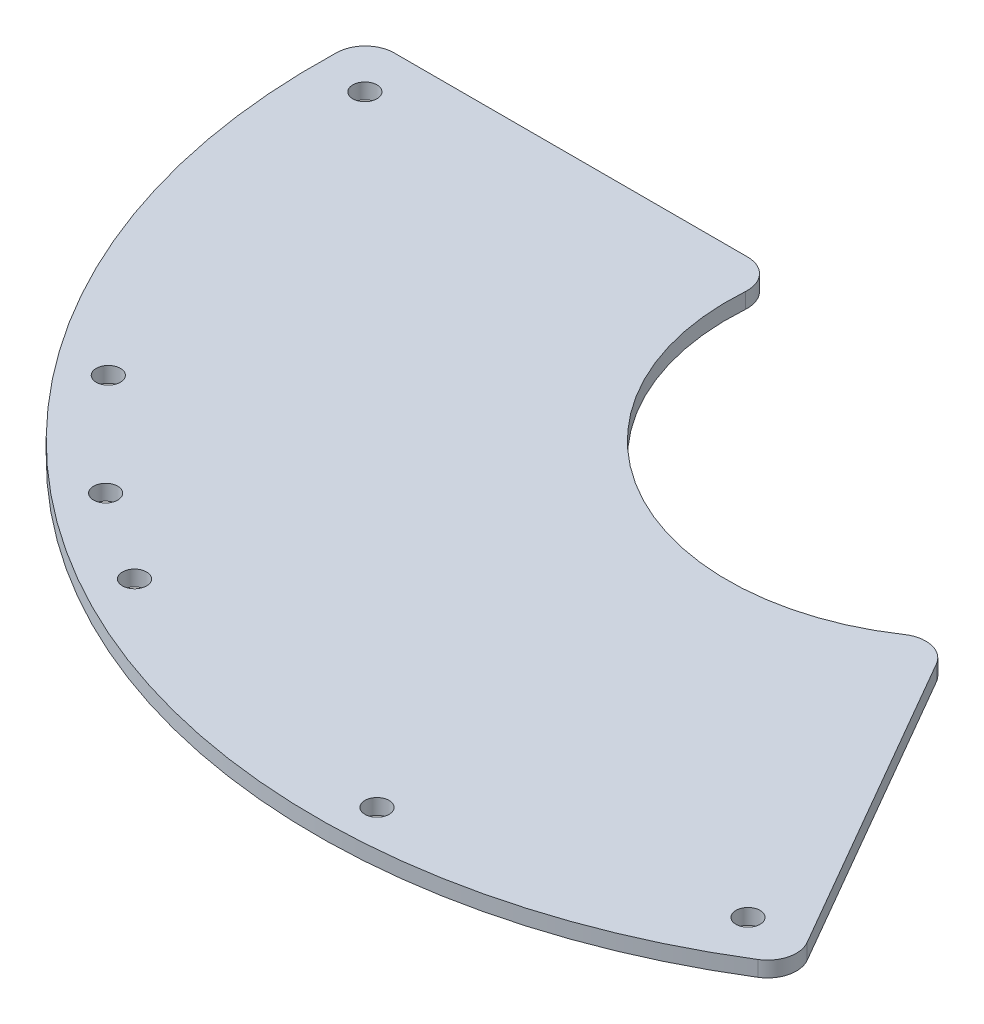
SolidWorks part; units mm, degrees
material "Thornel VCB-20 Carbon Cloth"
ref_plane "Front Plane" through (0, 0, 0) normal (0, 0, 1) x (1, 0, 0)
ref_plane "Top Plane" through (0, 0, 0) normal (0, 1, 0) x (1, 0, 0)
ref_plane "Right Plane" through (0, 0, 0) normal (1, 0, 0) x (0, 0, -1)
sketch "Sketch1" plane through (0, 0, 0) normal (0, 1, 0) x (1, 0, 0)
  line L0 (0, 0) -> (42.3981, -73.4357) construction
  line L1 (0, 0) -> (33.75, -58.4567) construction
  line L2 (0, 0) -> (-67.5, 0) construction
  line L3 (-67.3146, 5) -> (-24.4949, 5)
  line L4 (37.9874, -55.7961) -> (16.5776, -18.7132)
  line L5 (0, 0) -> (2.2161, -63.4613) construction
  line L6 (0, 0) -> (-30.7854, -55.5384) construction
  line L7 (0, 0) -> (-50.3779, -38.6564) construction
  line L8 (-39.9618, -49.3488) -> (0, 0) construction
  arc A0 (-67.3146, 5) -> (37.9874, -55.7961) centre (0, 0) ccw
  circle A2 centre (0, 0) radius 62.5 construction
  circle A3 centre (-62.5, 0) radius 1.25
  circle A4 centre (31.25, -54.1266) radius 1.25
  circle A5 centre (0, 0) radius 63.5 construction
  circle A6 centre (2.2161, -63.4613) radius 1.25
  circle A7 centre (-30.7854, -55.5384) radius 1.25
  circle A8 centre (-39.9618, -49.3488) radius 1.25
  circle A9 centre (-50.3779, -38.6564) radius 1.25
  arc A10 (-24.4949, 5) -> (16.5776, -18.7132) centre (0, 0) ccw
  dimension "D3" = 125
  dimension "D7" = 2.5
  dimension "D17" = 25
  dimension "D5" = 5
  dimension "D8" = 4
  dimension "D4" = 120
  dimension "D6" = 5
  dimension "D9" = 37.5
  dimension "D10" = 51
  dimension "D11" = 61
  dimension "D12" = 92
  dimension "D2" = 5
extrude "Boss-Extrude1" add sketch "Sketch1" along normal mid plane 1.6
fillet "Fillet1" radius 3 4 edges at (-67.3146, 0, -5) (37.9874, 0, 55.7961) (16.5776, 0, 18.7132) (-24.4949, 0, -5)
equation "\"pcb_mount_circle_diameter\"= 125mm"
equation "\"inner_diameter\"= 50mm"
equation "\"D3@Sketch1\"=\"pcb_mount_circle_diameter\""
equation "\"D17@Sketch1\"=\"inner_diameter\"/2"
equation "\"extra_overlap\"= 5mm"
equation "\"D2@Sketch1\"=\"extra_overlap\""
equation "\"D5@Sketch1\"=\"extra_overlap\""
equation "\"D6@Sketch1\"=\"extra_overlap\""
